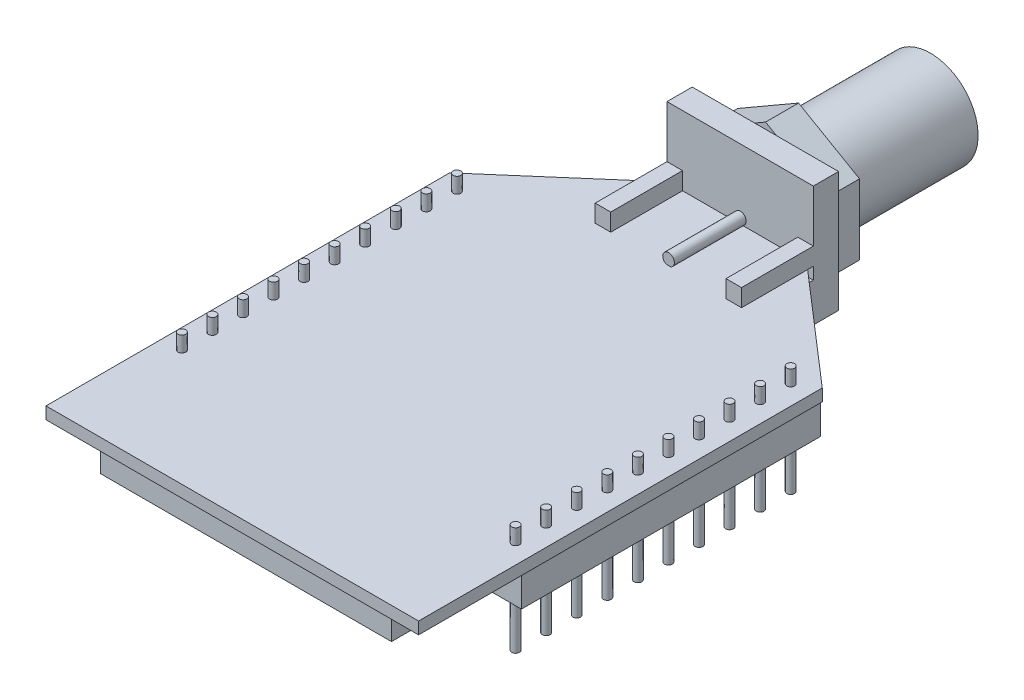
SolidWorks part; units mm, degrees
ref_plane "Front Plane" through (0, 0, 0) normal (0, 0, 1) x (1, 0, 0)
ref_plane "Top Plane" through (0, 0, 0) normal (0, 1, 0) x (1, 0, 0)
ref_plane "Right Plane" through (0, 0, 0) normal (1, 0, 0) x (0, 0, -1)
sketch "Sketch1" plane through (0, 0, 0) normal (0, 1, 0) x (1, 0, 0)
  line L0 (0, 26.416) -> (7.62, 33.02)
  line L1 (0, 0) -> (24.384, 0)
  line L2 (0, 0) -> (0, 26.416)
  line L3 (7.62, 33.02) -> (16.764, 33.02)
  line L4 (24.384, 0) -> (24.384, 26.416)
  line L5 (24.384, 26.416) -> (16.764, 33.02)
  dimension "D1" = 33.02
  dimension "D2" = 24.384
  dimension "D3" = 26.416
  dimension "D4" = 7.62
  dimension "D5" = 16.764
  dimension "D6" = 26.416
extrude "Base PCB" add sketch "Sketch1" along normal blind 0.7874
sketch "Sketch2" plane through (0, 0.7874, 0) normal (0, 1, 0) x (1, 0, 0)
  line L0 (0, 26.416) -> (0, 0) construction
  line L1 (0, 0) -> (24.384, 0) construction
  circle A0 centre (1.27, 7.62) radius 0.254
  dimension "D1" = 1.27
  dimension "D2" = 7.62
extrude "Header Hole" cut sketch "Sketch2" against normal through all
pattern_linear "2mm Header pattern" count 10 spacing 2 along (0, 0, -1) count 2 spacing 21.844 along (1, 0, 0) of "Header Hole"
sketch "Sketch3" plane through (0, 0, 0) normal (0, -1, 0) x (1, 0, 0)
  line L1 (2.794, -0.762) -> (21.844, -0.762)
  line L2 (2.794, -0.762) -> (2.794, -24.892)
  line L3 (2.794, -24.892) -> (21.844, -24.892)
  line L4 (21.844, -0.762) -> (21.844, -24.892)
extrude "Wireless Module" add sketch "Sketch3" along normal blind 2.032
sketch "Sketch12" plane through (0, 0.7874, 0) normal (0, 1, 0) x (1, 0, 0)
  circle A0 centre (1.27, 7.62) radius 0.254
extrude "Header Pin" add sketch "Sketch12" along normal blind 1.016 and the other way blind 6.096
pattern_linear "2mm Header Pin pattern" count 10 spacing 2 along (0, 0, -1) count 2 spacing 21.844 along (1, 0, 0) of "Header Pin"
sketch "Sketch13" plane through (0, 0, 0) normal (0, -1, 0) x (1, 0, 0)
  line L1 (22.098, -6.858) -> (24.257, -6.858)
  line L2 (22.098, -6.858) -> (22.098, -26.416)
  line L3 (22.098, -26.416) -> (24.257, -26.416)
  line L4 (24.257, -6.858) -> (24.257, -26.416)
extrude "Header Boss" add sketch "Sketch13" along normal up to surface (2.032 mm away) up to face at (12.319, -2.032, -12.827)
pattern_linear "Header Boss pattern" count 2 spacing 21.844 along (-1, 0, 0) of "Header Boss"
sketch "Sketch4" plane through (0, 0, -33.02) normal (0, 0, -1) x (-1, 0, 0)
  line L1 (-7.62, -2.54) -> (-17.1958, -2.54)
  line L2 (-7.62, -2.54) -> (-7.62, 5.334)
  line L3 (-7.62, 5.334) -> (-17.1958, 5.334)
  line L4 (-17.1958, -2.54) -> (-17.1958, 5.334)
extrude "SMA Base" add sketch "Sketch4" along normal blind 1.651
sketch "Sketch5" plane through (0, 0, -33.02) normal (0, 0, 1) x (1, 0, 0)
  line L0 (0, 0) -> (24.384, 0) construction
  line L1 (7.62, -2.54) -> (8.636, -2.54)
  line L2 (7.62, -2.54) -> (7.62, 0)
  line L3 (7.62, 0) -> (8.636, 0)
  line L4 (8.636, -2.54) -> (8.636, 0)
  line L6 (17.1958, -2.54) -> (16.1798, -2.54)
  line L7 (17.1958, -2.54) -> (17.1958, 0)
  line L8 (17.1958, 0) -> (16.1798, 0)
  line L9 (16.1798, -2.54) -> (16.1798, 0)
  dimension "D1" = 1.016
  dimension "D2" = 1.016
extrude "SMA Prongs-bottom" add sketch "Sketch5" along normal blind 4.699
sketch "Sketch6" plane through (0, 0, -33.02) normal (0, 0, 1) x (1, 0, 0)
  line L0 (17.1958, 5.334) -> (17.1958, 0) construction
  line L1 (7.62, 0.7874) -> (8.636, 0.7874)
  line L2 (7.62, 0.7874) -> (7.62, 1.9304)
  line L3 (7.62, 1.9304) -> (8.636, 1.9304)
  line L4 (8.636, 0.7874) -> (8.636, 1.9304)
  line L5 (17.1958, 0.7874) -> (16.1798, 0.7874)
  line L6 (17.1958, 0.7874) -> (17.1958, 1.9304)
  line L7 (17.1958, 1.9304) -> (16.1798, 1.9304)
  line L8 (16.1798, 0.7874) -> (16.1798, 1.9304)
  line L9 (0, 0.7874) -> (24.384, 0.7874) construction
  dimension "D1" = 1.016
  dimension "D2" = 1.016
  dimension "D3" = 1.143
  dimension "D4" = 1.143
extrude "SMA Prongs-top" add sketch "Sketch6" along normal blind 4.699
sketch "Sketch7" plane through (0, 0, -33.02) normal (0, 0, 1) x (1, 0, 0)
  circle A0 centre (12.4206, 1.143) radius 0.381
extrude "SMA Center Pin" add sketch "Sketch7" along normal blind 4.699 and the other way blind 13.208
sketch "Sketch9" plane through (0, 0, -34.671) normal (0, 0, -1) x (-1, 0, 0)
  line L1 (-12.4206, 5.7477) -> (-16.4084, 3.4454)
  line L2 (-16.4084, 3.4454) -> (-16.4084, -1.1594)
  line L3 (-16.4084, -1.1594) -> (-12.4206, -3.4617)
  line L4 (-12.4206, -3.4617) -> (-8.4328, -1.1594)
  line L5 (-8.4328, -1.1594) -> (-8.4328, 3.4454)
  line L6 (-8.4328, 3.4454) -> (-12.4206, 5.7477)
  circle A0 centre (-12.4206, 1.143) radius 3.9878 construction
extrude "SMA Nut" add sketch "Sketch9" along normal blind 2.159
sketch "Sketch10" plane through (0, 0, -36.83) normal (0, 0, -1) x (-1, 0, 0)
  circle A0 centre (-12.4206, 1.143) radius 3.1115
extrude "RPSMA Barrel" add sketch "Sketch10" along normal blind 8.636
sketch "Sketch11" plane through (0, 0, -45.466) normal (0, 0, -1) x (-1, 0, 0)
  circle A0 centre (-12.4206, 1.143) radius 2.286
  circle A1 centre (-12.4206, 1.143) radius 0.381
extrude "Cut-Extrude4" cut sketch "Sketch11" against normal blind 2.032
